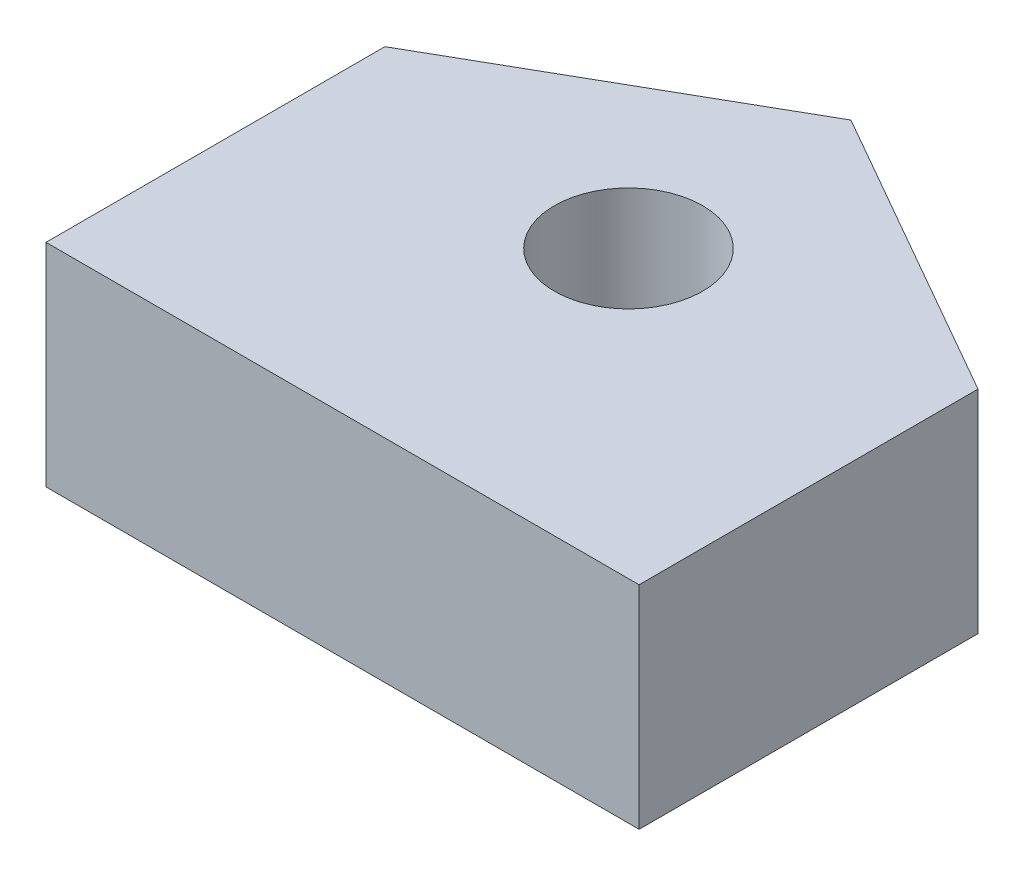
SolidWorks part; units mm, degrees
ref_plane "Front Plane" through (0, 0, 0) normal (0, 0, 1) x (1, 0, 0)
ref_plane "Top Plane" through (0, 0, 0) normal (0, 1, 0) x (1, 0, 0)
ref_plane "Right Plane" through (0, 0, 0) normal (1, 0, 0) x (0, 0, -1)
sketch "Sketch2" plane through (0, 0, 0) normal (0, 1, 0) x (1, 0, 0)
  line L2 (-214, -48.75) -> (-207, -44.75) construction
  line L3 (-207, -44.75) -> (-200, -48.75) construction
  line L5 (-200, -56.75) -> (-202, -56.75) construction
  line L6 (-212, -56.75) -> (-212, -61.75) construction
  line L7 (-212, -61.75) -> (-202, -61.75) construction
  line L8 (-202, -61.75) -> (-202, -56.75) construction
  line L9 (-212, -56.75) -> (-214, -56.75) construction
  line L10 (-214, -56.75) -> (-214, -48.75) construction
  line L11 (-234, -23.478) -> (-234, -61.4421) construction
  line L17 (-268, -48.75) -> (-268, -56.75)
  line L18 (-261, -44.75) -> (-268, -48.75)
  line L19 (-254, -48.75) -> (-261, -44.75)
  line L20 (-254, -56.75) -> (-254, -48.75)
  line L21 (-268, -56.75) -> (-254, -56.75)
  line L22 (-200, -48.75) -> (-200, -56.75) construction
  circle A0 centre (-207, -50) radius 1.75 construction
  circle A1 centre (-261, -50) radius 1.75
  point P12 (-207, -61.75)
  dimension "D8" = 3.5
  dimension "D1" = 10
  dimension "D2" = 5
  dimension "D3" = 2
  dimension "D4" = 4
  dimension "D5" = 8
  dimension "D6" = 8
  dimension "D7" = 6.75
  dimension "D9" = 202
  dimension "D10" = 50
  dimension "D11" = 20
extrude "Boss-Extrude3" add sketch "Sketch2" along normal blind 5 separate body
